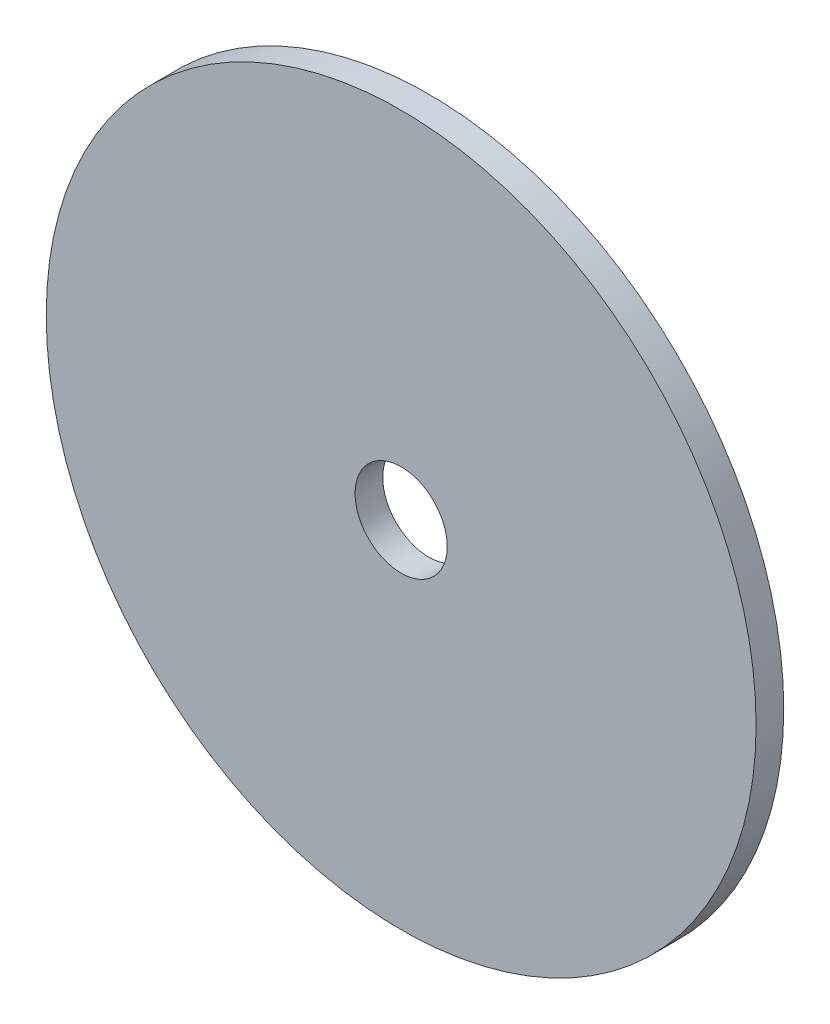
SolidWorks part; units mm, degrees
ref_plane "Alzado" through (0, 0, 0) normal (0, 0, 1) x (1, 0, 0)
ref_plane "Planta" through (0, 0, 0) normal (0, 1, 0) x (1, 0, 0)
ref_plane "Vista lateral" through (0, 0, 0) normal (1, 0, 0) x (0, 0, -1)
sketch "Croquis1" plane through (0, 0, 0) normal (0, 0, 1) x (1, 0, 0)
  circle A0 centre (0, 0) radius 77
  dimension "D1" = 154
extrude "Saliente-Extruir1" add sketch "Croquis1" along normal blind 6
sketch "Croquis2" plane through (0, 0, 6) normal (0, 0, 1) x (1, 0, 0)
  circle A0 centre (0, 0) radius 10
extrude "Cortar-Extruir1" cut sketch "Croquis2" against normal blind 36 contours A0
